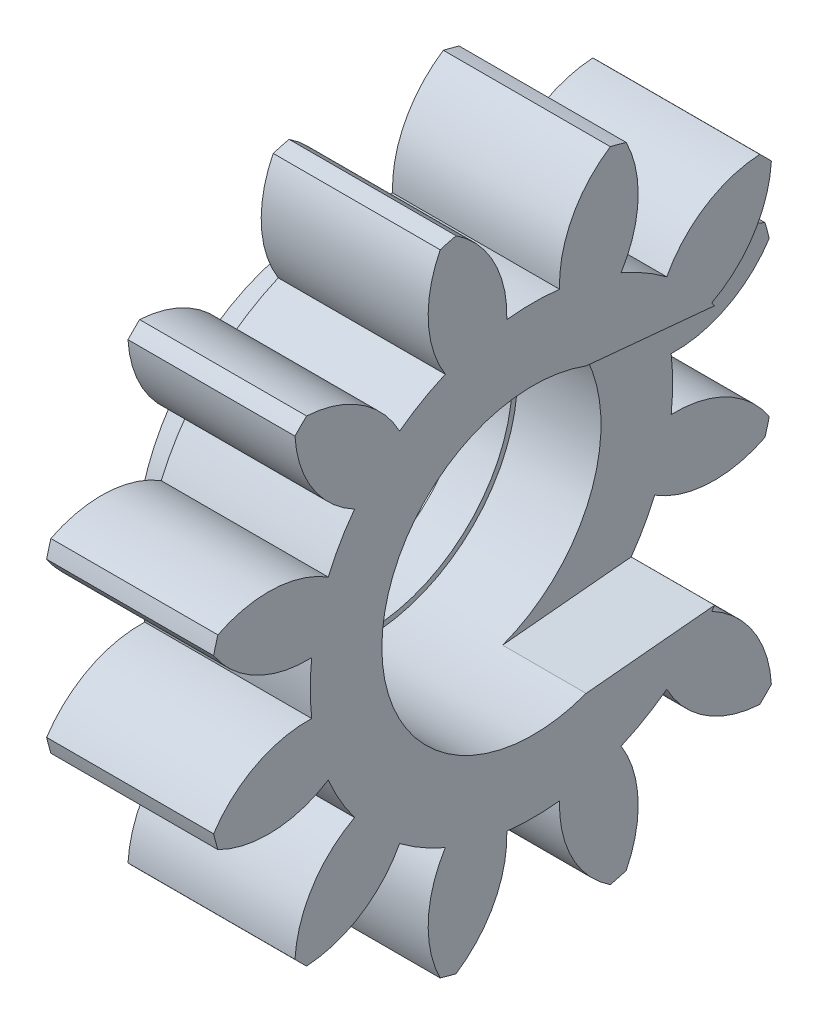
SolidWorks part; units mm, degrees
material "PLA"
ref_plane "Plane1" through (0, 0, 0) normal (0, 0, 1) x (1, 0, 0)
ref_plane "Plane2" through (0, 0, 0) normal (0, 1, 0) x (1, 0, 0)
ref_plane "Plane3" through (0, 0, 0) normal (1, 0, 0) x (0, 0, -1)
other "Configuration Table"
sketch "HoldingSke" plane through (0, 0, 0) normal (0, 1, 0) x (1, 0, 0)
  line L0 (0, 0) -> (0.8695, -0.1848)
  line L1 (-15, 0) -> (100, 0) construction
  line L2 (0, 0) -> (-2.1039, 2.3779)
  line L3 (0, 0) -> (-11.863, 4.5341)
  line L4 (0, 0) -> (8.4473, 1.7955)
  line L5 (0, 0) -> (-46.8476, -17.4728)
  line L6 (0, 0) -> (-3.3159, -2.2372)
  line L7 (-2.1039, 2.3779) -> (8.6586, 51.2059)
  line L8 (-76.2, 54.61) -> (-75.7, 54.61)
  line L9 (-71.009, 38.7566) -> (-53.1078, 45.2721)
  line L10 (-76.2, 71.12) -> (104.1128, 71.12)
  line L11 (0, 0) -> (-4, 0)
  line L12 (-76.2, 101.6) -> (-76.158, 101.6)
  line L13 (24.9733, 27.94) -> (52.9518, 28.4284)
  line L14 (24.9733, 27.94) -> (24.9743, 27.94)
  line L15 (24.9733, 27.94) -> (100.4006, 29.5858)
  line L16 (-63.627, -1.125) -> (-12.827, -1.125)
  circle A0 centre (0, 0) radius 1.5
  circle A1 centre (0, 0) radius 5.3427
  circle A2 centre (0, 0) radius 37.5
  circle A3 centre (0, 0) radius 1.5
  dimension "MHD" = 10.6855
  dimension "Hub_dia" = 75
  dimension "Bore" = 3
  dimension "MBD" = 3
  dimension "Num_teeth" = 12
  dimension "Pitch" = 0.8889
  dimension "Overall_len" = 50
  dimension "Show_teeth" = 12
  dimension "Thickness" = 4
  dimension "OAL" = 50.0001
  dimension "T_dim" = 0.5
  dimension "Ap" = 20
  dimension "H" = 19.05
  dimension "Pitch_radius" = 180.3128
  dimension "Width" = 4
  dimension "Backlash" = 0.042
  dimension "Addendum_fac" = 1
  dimension "Dedendum_fac" = 1.25
  dimension "Clearance_fac" = 0.25
  dimension "Dedendum_add" = 0.001
  dimension "Module" = 1.125
sketch "BasProSke" plane through (0, 0, 0) normal (0, 1, 0) x (1, 0, 0)
  line L0 (-10, 0) -> (60, 0) construction
  line L1 (0, 0) -> (0, 7.875)
  line L2 (0, 0) -> (4, 0)
  line L3 (4, 0) -> (4, 7.875)
  line L4 (4, 7.875) -> (0, 7.875)
  dimension "Thickness" = 4
  dimension "Diameter" = 15.75
revolve "Base-Revolve" add sketch "BasProSke" angle 360 about L0
sketch "TooCutSke" plane through (0, 0, 0) normal (1, 0, 0) x (0, 0, -1)
  line L1 (0, 0) -> (0, 107) construction
  line L2 (0, 0) -> (-0.9544, 6.6822) construction
  line L3 (0, 0) -> (-3.469, 12.9463) construction
  line L4 (-0.9544, 6.6822) -> (-1.7345, 6.4732) construction
  arc A0 (0.6314, 5.3053) -> (-0.6314, 5.3053) centre (0, 0) ccw
  arc A1 (1.8767, 7.6743) -> (-1.8767, 7.6743) centre (0, 0) ccw
  circle A2 centre (0, 0) radius 6.75 construction
  circle A3 centre (0, 0) radius 6.3429 construction
  arc A4 (-0.6314, 5.3053) -> (-1.8767, 7.6743) centre (-3.3298, 5.3986) ccw
  arc A5 (1.8767, 7.6743) -> (0.6314, 5.3053) centre (3.3298, 5.3986) ccw
  dimension "Root_dia" = 10.6855
  dimension "Overcut_dia" = 15.8008
  dimension "Pitch_dia" = 13.5
  dimension "Base_dia" = 12.6859
  dimension "Flank_rad" = 2.7
  dimension "Half_ang" = 15
  dimension "Half_CT" = 0.8076
extrude "ToothCut" cut sketch "TooCutSke" along normal through all
fillet "Breaks" [suppressed] radius 0.0225
fillet "RootFillets" [suppressed] radius 0.2823
pattern_circular "TeethCuts" count 12 every 30 about axis through (-10, 0, 0) along (1, 0, 0) of "ToothCut", "RootFillets", "Breaks"
sketch "HubNeaOneSke" plane through (0, 0, 0) normal (-1, 0, 0) x (0, 0, 1)
  circle A0 centre (0, 0) radius 5.3427
  dimension "Diameter" = 10.6855
extrude "HubNearOne" [suppressed] add sketch "HubNeaOneSke" along normal blind 46.0001
sketch "HubNeaBotSke" plane through (0, 0, 0) normal (-1, 0, 0) x (0, 0, 1)
  circle A0 centre (0, 0) radius 5.3427
  dimension "Diameter" = 10.6855
extrude "HubNearBoth" [suppressed] add sketch "HubNeaBotSke" along normal blind 23
ref_plane "FarPln" through (4, 0, 0) normal (1, 0, 0) x (0, 0, -1)
sketch "HubFarSke" plane through (4, 0, 0) normal (1, 0, 0) x (0, 0, -1)
  circle A0 centre (0, 0) radius 5.3427
  dimension "Diameter" = 10.6855
extrude "HubFar" [suppressed] add sketch "HubFarSke" along normal blind 23
sketch "BorSke" plane through (0, 0, 0) normal (1, 0, 0) x (0, 0, -1)
  circle A0 centre (0, 0) radius 3.625
  dimension "Diameter" = 7.25
extrude "Bore" cut sketch "BorSke" along normal mid plane 100.0001
sketch "KeySke" plane through (0, 0, 0) normal (1, 0, 0) x (0, 0, -1)
  line L0 (-0.6, 0) -> (-0.6, 2)
  line L1 (-0.6, 2) -> (0.6, 2)
  line L2 (0.6, 2) -> (0.6, 0)
  line L3 (0, 0) -> (0, 34) construction
  line L4 (-0.6, 0) -> (0.6, 0)
  dimension "Offset" = 2
  dimension "Width" = 1.2
extrude "Keyway" [suppressed] cut sketch "KeySke" along normal mid plane 100.0001
pattern_circular "Keyway2" [suppressed] count 2 every 90 about axis through (-10, 0, 0) along (1, 0, 0)
sketch "Sketch1" plane through (0, 0, 0) normal (-1, 0, 0) x (0, 0, 1)
  circle A0 centre (0, 0) radius 3.5
  circle A1 centre (0, 0) radius 4.5
  dimension "D1" = 7
  dimension "D2" = 1
extrude "Boss-Extrude1" add sketch "Sketch1" along normal blind 1
sketch "Sketch3" plane through (4, 0, 0) normal (1, 0, 0) x (0, 0, -1)
  line L0 (0, 13.25) -> (0, -13.25) construction
  line L1 (18, 0) -> (-3.5, 0) construction
  line L2 (-13.25, 0) -> (13.25, 0) construction
  line L3 (0.3281, 3.4846) -> (16.1875, 1.9912)
  line L5 (16.1875, -1.9912) -> (0.3281, -3.4846)
  arc A0 (0.3281, 3.4846) -> (0.3281, -3.4846) centre (0, 0) ccw
  arc A1 (16.1875, -1.9912) -> (16.1875, 1.9912) centre (16, 0) ccw
  point P6 (0, 0)
  dimension "D2" = 7
  dimension "D3" = 4
  dimension "D1" = 26.5
  dimension "D4" = 21.5
extrude "Cut-Extrude2" cut sketch "Sketch3" against normal offset from surface (2 mm away) 3 up to face at (-1, 0, 4.5)
equation "' \"Module@HoldingSke\" = 6.35"
equation "' \"Num_teeth@HoldingSke\" = 12"
equation "' \"Ap@HoldingSke\" =  20"
equation "' \"Ap@HoldingSke\" = 20"
equation "' \"Width@HoldingSke\" = 0.5 * 25.4"
equation "' \"Hub_dia@HoldingSke\"= 1 * 25.4"
equation "' \"Hub_dia@HoldingSke\" = 1 * 25.4"
equation "' \"Overall_len@HoldingSke\" = 1.0 * 25.4"
equation "' \"Bore@HoldingSke\" = 0.75 * 25.4"
equation "' \"T_dim@HoldingSke\" = 0.1 * 25.4"
equation "' \"Width@KeySke\" = 0.25 * 25.4"
equation "' \"Show_teeth@HoldingSke\" = 13"
equation "' \"Backlash@HoldingSke\" = 0.009 * 25.4"
equation "' \"Addendum_fac@HoldingSke\" = 1.0"
equation "' \"Dedendum_fac@HoldingSke\" = 1.25"
equation "' \"Dedendum_add@HoldingSke\" = 0.00005 * 25.4"
equation "' \"Clearance_fac@HoldingSke\" = 0.25"
equation "\"Pitch@HoldingSke\" = 1 / \"Module@HoldingSke\""
equation "\"Overcut_dia@TooCutSke\" = (\"Num_teeth@HoldingSke\" + 2 * \"Addendum_fac@HoldingSke\") / \"Pitch@HoldingSke\" + 0.002 * 25.4"
equation "\"Pitch_dia@TooCutSke\" = \"Num_teeth@HoldingSke\" / \"Pitch@HoldingSke\""
equation "\"Base_dia@TooCutSke\" = \"Num_teeth@HoldingSke\" / \"Pitch@HoldingSke\" * cos((\"Ap@HoldingSke\"  * 3.14159265 / 180))"
equation "\"Root_dia@TooCutSke\" = (\"Num_teeth@HoldingSke\" + 2) / \"Pitch@HoldingSke\" - 2 * (\"Addendum_fac@HoldingSke\" + \"Dedendum_fac@HoldingSke\") / \"Pitch@HoldingSke\" - \"Dedendum_add@HoldingSke\" * 2"
equation "\"Half_ang@TooCutSke\" = 180 / \"Num_teeth@HoldingSke\""
equation "\"Half_CT@TooCutSke\" = \"Num_teeth@HoldingSke\" / \"Pitch@HoldingSke\" * sin((3.14159265 / 2 / \"Num_teeth@HoldingSke\")) / 2 - 7 * \"Backlash@HoldingSke\" / 4"
equation "\"Flank_rad@TooCutSke\" = \"Num_teeth@HoldingSke\" / \"Pitch@HoldingSke\" / 5"
equation "\"Radius@RootFillets\" = \"Clearance_fac@HoldingSke\" / \"Pitch@HoldingSke\" + \"Dedendum_add@HoldingSke\""
equation "\"Break_rad@Breaks\" = 0.02 / \"Pitch@HoldingSke\""
equation "\"Thickness@HoldingSke\" = \"Width@HoldingSke\""
equation "\"OAL@HoldingSke\" = \"Thickness@HoldingSke\""
equation "\"MHD@HoldingSke\" = (\"Num_teeth@HoldingSke\" + 2) / \"Pitch@HoldingSke\" - 2 * (\"Addendum_fac@HoldingSke\" + \"Dedendum_fac@HoldingSke\")  / \"Pitch@HoldingSke\" - \"Dedendum_add@HoldingSke\" * 2"
equation "\"MBD@HoldingSke\" = (\"Num_teeth@HoldingSke\" + 2) / \"Pitch@HoldingSke\" - 2 * (\"Addendum_fac@HoldingSke\" + \"Dedendum_fac@HoldingSke\")  / \"Pitch@HoldingSke\" - \"Dedendum_add@HoldingSke\" * 2 - 0.002 * 25.4"
equation "\"MHD@HoldingSke\" = ((sgn( \"MHD@HoldingSke\" - \"Hub_dia@HoldingSke\" )-1)*( \"MHD@HoldingSke\" - \"Hub_dia@HoldingSke\" ))/-2+ \"Hub_dia@HoldingSke\""
equation "\"MBD@HoldingSke\" = ((sgn( \"MBD@HoldingSke\" - \"Bore@HoldingSke\" )-1)*( \"MBD@HoldingSke\" - \"Bore@HoldingSke\" ))/-2+ \"Bore@HoldingSke\""
equation "\"OAL@HoldingSke\" = ((sgn( \"OAL@HoldingSke\" - \"Overall_len@HoldingSke\" )+1)*( \"OAL@HoldingSke\" - \"Overall_len@HoldingSke\" ))/2 + \"Overall_len@HoldingSke\" + 0.000002 * 25.4"
equation "\"Num_teeth@TeethCuts\" = int( \"Show_teeth@HoldingSke\" ) + 1"
equation "\"Num_teeth@TeethCuts\" = ((sgn( \"Num_teeth@TeethCuts\" - \"Num_teeth@HoldingSke\" )-1)*( \"Num_teeth@TeethCuts\" - \"Num_teeth@HoldingSke\" ))/-2+ \"Num_teeth@HoldingSke\""
equation "\"Num_teeth@TeethCuts\" = ((sgn( \"Num_teeth@TeethCuts\" - 2.0)+1)*( \"Num_teeth@TeethCuts\" - 2.0))/2 +2.0"
equation "\"Angle@TeethCuts\" = 360.0 / \"Num_teeth@HoldingSke\""
equation "\"Diameter@BasProSke\" = (\"Num_teeth@HoldingSke\" + 2 * \"Addendum_fac@HoldingSke\") / \"Pitch@HoldingSke\""
equation "\"Thickness@BasProSke\"  = \"Thickness@HoldingSke\""
equation "' \"Fillet_rad@BasProSke\" =  \"Thickness@HoldingSke\" * 0.05"
equation "' \"Fillet_rad@BasProSke\" = \"Thickness@HoldingSke\" * 0.05"
equation "\"MHD@HoldingSke\" = ((sgn( \"MHD@HoldingSke\" - \"Root_dia@TooCutSke\" )-1)*( \"MHD@HoldingSke\" - \"Root_dia@TooCutSke\" ))/-2+ \"Root_dia@TooCutSke\""
equation "\"Diameter@HubNeaOneSke\" = \"MHD@HoldingSke\""
equation "\"Length@HubNearOne\" = \"OAL@HoldingSke\" - \"Thickness@BasProSke\""
equation "\"Diameter@HubNeaBotSke\" = \"MHD@HoldingSke\""
equation "\"Length@HubNearBoth\" = ( \"OAL@HoldingSke\" - \"Thickness@BasProSke\" ) / 2.0"
equation "\"Thickness@FarPln\" = \"Thickness@BasProSke\""
equation "\"Diameter@HubFarSke\" = \"MHD@HoldingSke\""
equation "\"Length@HubFar\" = ( \"OAL@HoldingSke\" - \"Thickness@BasProSke\" ) / 2.0"
equation "\"D1@Bore\" = \"OAL@HoldingSke\" * 2.0"
equation "\"D1@Keyway\" = \"OAL@HoldingSke\" * 2.0"
equation "\"Offset@KeySke\" = \"T_dim@HoldingSke\" + \"MBD@HoldingSke\" / 2.0"
